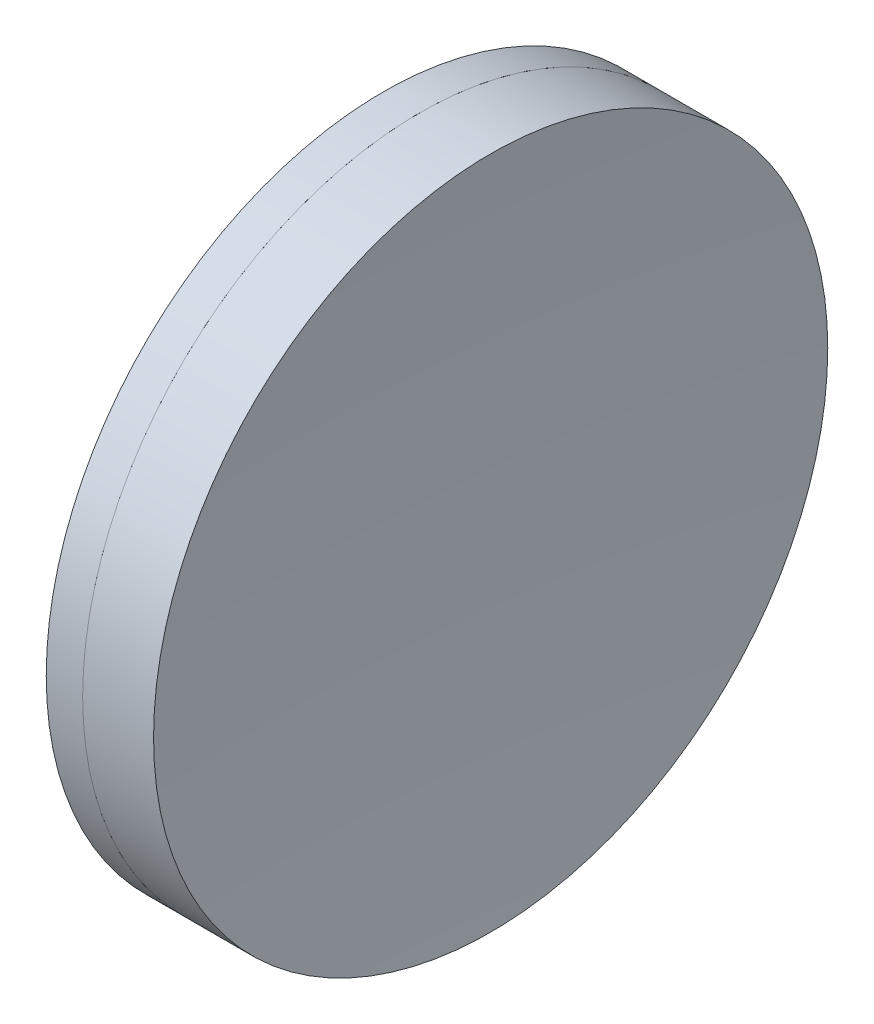
SolidWorks part; units mm, degrees
ref_plane "前视基准面" through (0, 0, 0) normal (0, 0, 1) x (1, 0, 0)
ref_plane "上视基准面" through (0, 0, 0) normal (0, 1, 0) x (1, 0, 0)
ref_plane "右视基准面" through (0, 0, 0) normal (1, 0, 0) x (0, 0, -1)
sketch "草图1" plane through (0, 0, 0) normal (0, 1, 0) x (1, 0, 0)
  line L0 (-0.8161, 0) -> (405.8749, 0) construction
  line L1 (316.4529, -25.4) -> (319.1969, -25.4)
  line L2 (316.4529, 25.4) -> (319.1969, 25.4)
  arc A0 (319.1969, -25.4) -> (319.1969, 25.4) centre (86.3079, 0) ccw
  arc A1 (316.4529, 25.4) -> (316.4529, -25.4) centre (487.5579, 0) ccw
  point P4 (405.8749, 0)
  point P10 (314.5779, 0)
  point P11 (320.5779, 0)
  dimension "D3" = 172.98
  dimension "D4" = 234.27
  dimension "D1" = 25.4
  dimension "D2" = 25.4
  dimension "D5" = 6
revolve "旋转1" add sketch "草图1" angle 360 about L0
sketch "草图2" plane through (0, 0, 0) normal (0, 1, 0) x (1, 0, 0)
  line L0 (-0.5519, 0) -> (390.9472, 0) construction
  line L2 (319.1969, 25.4) -> (324.5393, 25.4)
  line L3 (319.1969, -25.4) -> (324.5393, -25.4)
  arc A0 (324.5393, 25.4) -> (324.5393, -25.4) centre (659.5779, 0) ccw
  arc A1 (319.1969, -25.4) -> (319.1969, 25.4) centre (86.3079, 0) ccw construction
  arc A2 (319.1969, -25.4) -> (319.1969, 25.4) centre (86.3079, 0) ccw
  point P4 (320.5779, 0)
  point P8 (323.5779, 0)
  point P9 (390.9472, 0)
  dimension "D1" = 336
  dimension "D2" = 3
revolve "旋转2" add sketch "草图2" angle 360 about L0
